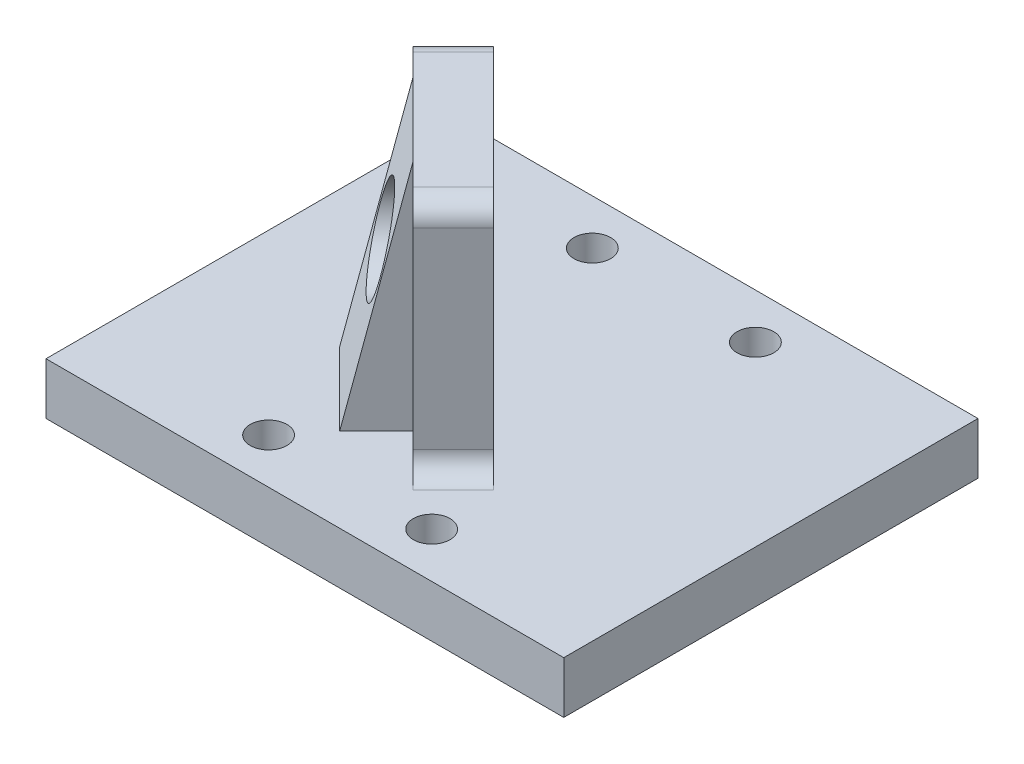
SolidWorks part; units mm, degrees
material "PLA Black"
ref_plane "Front Plane" through (0, 0, 0) normal (0, 0, 1) x (1, 0, 0)
ref_plane "Top Plane" through (0, 0, 0) normal (0, 1, 0) x (1, 0, 0)
ref_plane "Right Plane" through (0, 0, 0) normal (1, 0, 0) x (0, 0, -1)
sketch "Sketch1" plane through (0, 0, 0) normal (0, 1, 0) x (1, 0, 0)
  line L1 (-31.75, -25.4) -> (31.75, -25.4)
  line L2 (-31.75, -25.4) -> (-31.75, 25.4)
  line L3 (-31.75, 25.4) -> (31.75, 25.4)
  line L4 (31.75, -25.4) -> (31.75, 25.4)
  line L5 (-31.75, -25.4) -> (31.75, 25.4) construction
  line L6 (-31.75, 25.4) -> (31.75, -25.4) construction
  point P0 (0, 0)
  dimension "D1" = 63.5
  dimension "D2" = 50.8
extrude "Boss-Extrude1" add sketch "Sketch1" along normal blind 6.35
sketch "Sketch2" plane through (0, 6.35, 0) normal (0, 1, 0) x (1, 0, 0)
  line L0 (2.908, -15.0525) -> (-15.0525, 2.908)
  line L1 (2.908, -15.0525) -> (7.8577, -10.1028)
  line L2 (-15.0525, 2.908) -> (-10.1028, 7.8577)
  line L3 (7.8577, -10.1028) -> (-10.1028, 7.8577)
  line L4 (2.908, -15.0525) -> (-10.1028, 7.8577) construction
  line L5 (-15.0525, 2.908) -> (7.8577, -10.1028) construction
  line L6 (31.75, 25.4) -> (-31.75, 25.4) construction
  line L7 (0, 0) -> (-35355.3391, 35355.3391) construction
  line L8 (-3.5974, -3.5974) -> (0, 0) construction
  point P1 (-3.5974, -3.5974)
  dimension "D1" = 3.175
  dimension "D2" = 25.4
  dimension "D3" = 7
  dimension "D4" = 135
extrude "Boss-Extrude2" add sketch "Sketch2" along normal blind 28.575
ref_plane "Plane1" through (0, 0, 0) normal (0.7071, 0, -0.7071) x (-0.7071, 0, -0.7071)
sketch "Sketch4" plane through (0, 6.35, 0) normal (0, 1, 0) x (1, 0, 0)
  line L4 (-10, -19.85) -> (10, 19.85) construction
  circle A0 centre (10, -19.85) radius 2.25
  circle A1 centre (10, 19.85) radius 2.25
  circle A2 centre (-10, 19.85) radius 2.25
  circle A3 centre (-10, -19.85) radius 2.25
  point P8 (0, 0)
  dimension "D2" = 4.5
  dimension "D1" = 39.7
  dimension "D5" = 20
extrude "Cut-Extrude2" cut sketch "Sketch4" against normal through all
fillet "Fillet1" radius 2.54 4 edges at (-12.5777, 6.35, -5.3828) (-12.5777, 34.925, -5.3828) (5.3828, 34.925, 12.5777) (5.3828, 6.35, 12.5777)
sketch "Sketch5" plane through (-1.1225, 0, 1.1225) normal (0.7071, 0, -0.7071) x (-0.7071, 0, -0.7071)
  line L0 (-10.16, 34.925) -> (10.16, 34.925) construction
  circle A0 centre (0, 22.225) radius 2.413
  point P6 (0, 34.925)
  dimension "D1" = 4.826
  dimension "D2" = 12.7
ref_plane "Plane2" through (0, 0, 0) normal (-0.7071, 0, -0.7071) x (-0.7071, 0, 0.7071)
extrude "Cut-Extrude3" cut sketch "Sketch5" against normal through all
sketch "Sketch6" plane through (0, 0, 0) normal (-0.7071, 0, -0.7071) x (-0.7071, 0, 0.7071)
  line L0 (8.5875, 34.925) -> (14.9375, 6.35)
  line L1 (14.9375, 6.35) -> (8.5875, 6.35)
  line L2 (8.5875, 6.35) -> (8.5875, 34.925)
  dimension "D1" = 6.35
extrude "Boss-Extrude3" add sketch "Sketch6" along normal mid plane 12.7
sketch "Sketch7" plane through (-6.0723, 0, 6.0723) normal (-0.7071, 0, 0.7071) x (0.7071, 0, 0.7071)
  circle A0 centre (0, 22.225) radius 2.413 construction
  circle A1 centre (0, 22.225) radius 2.413 construction
  circle A2 centre (0, 22.225) radius 5.588
  dimension "D1" = 3.175
extrude "Cut-Extrude4" cut sketch "Sketch7" along normal through all
